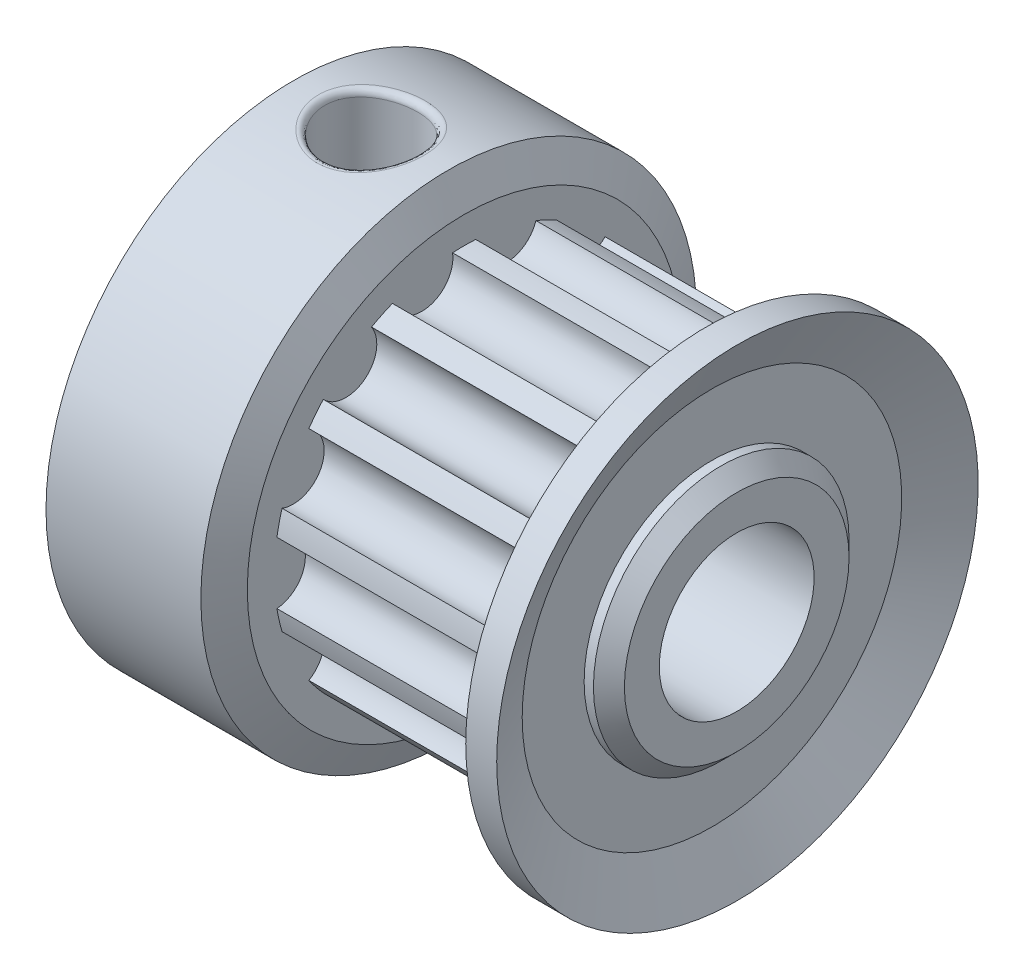
SolidWorks part; units mm, degrees
ref_plane "Ön Düzlem" through (0, 0, 0) normal (0, 0, 1) x (1, 0, 0)
ref_plane "Üst Düzlem" through (0, 0, 0) normal (0, 1, 0) x (1, 0, 0)
ref_plane "Sağ Düzlem" through (0, 0, 0) normal (1, 0, 0) x (0, 0, -1)
sketch "Çizim1" plane through (0, 0, 0) normal (0, 0, 1) x (1, 0, 0)
  line L0 (0, 9.9827) -> (0, -9.9827) construction
  line L1 (0, 0) -> (29.9605, 0) construction
  line L2 (0, 7) -> (0, 3.9)
  line L3 (0.1, 3.8) -> (0.3, 3.8)
  line L4 (0.3, 3.8) -> (0, 3.5)
  line L5 (0, 3.5) -> (0, 0)
  line L6 (0, 0) -> (14.8, 0)
  line L7 (14.8, 0) -> (14.8, 1.8873)
  line L10 (0, 7) -> (0.5, 8)
  line L11 (0.5, 8) -> (5.5, 8)
  line L12 (5.5, 8) -> (6, 7)
  line L13 (6, 7) -> (6, 6.1264)
  line L14 (6, 6.1264) -> (13, 6.1264)
  line L15 (13, 6.1264) -> (13.8229, 7.7721)
  line L18 (13.8229, 7.7721) -> (14.8229, 7.7721)
  line L19 (14.8229, 7.7721) -> (14, 6.1264)
  line L24 (14.8, 3.6264) -> (14.8, 1.8873)
  line L25 (14, 6.1264) -> (14, 4.1264)
  line L26 (14, 4.1264) -> (14.3, 4.1264)
  line L27 (14.3, 4.1264) -> (14.8, 3.6264)
  arc A0 (0, 3.9) -> (0.1, 3.8) centre (0.1, 3.9) ccw
  point P4 (0, 0)
  point P9 (14.8, 4.1264)
  point P33 (0, 3.8)
  dimension "D13" = 0.1
  dimension "D1" = 14.8
  dimension "D2" = 1
  dimension "D3" = 8
  dimension "D4" = 1.84
  dimension "D5" = 5
  dimension "D6" = 6
  dimension "D7" = 0.5
  dimension "D8" = 0.5
  dimension "D9" = 1
  dimension "D10" = 3.2
  dimension "D11" = 0.3
  dimension "D12" = 0.3
  dimension "D14" = 7
  dimension "D15" = 2
revolve "Döndür1" add sketch "Çizim1" angle 360 about L6
sketch "Çizim2" plane through (0, 0, 0) normal (-1, 0, 0) x (0, 0, 1)
  circle A0 centre (0, 0) radius 2.5
  dimension "D1" = 5
extrude "Kes-Ekstrüzyon1" cut sketch "Çizim2" against normal through all
sketch "Çizim3" plane through (6, 0, 0) normal (1, 0, 0) x (0, 0, -1)
  line L0 (0, 0) -> (6.1264, 0) construction
  circle A0 centre (0, 0) radius 6.1264 construction
  circle A1 centre (6.1264, 0) radius 1
  circle A2 centre (5.5197, -2.6581) radius 1
  circle A3 centre (3.8197, -4.7898) radius 1
  circle A4 centre (1.3632, -5.9728) radius 1
  circle A5 centre (-1.3632, -5.9728) radius 1
  circle A6 centre (-3.8197, -4.7898) radius 1
  circle A7 centre (-5.5197, -2.6581) radius 1
  circle A8 centre (-6.1264, 0) radius 1
  circle A9 centre (-5.5197, 2.6581) radius 1
  circle A10 centre (-3.8197, 4.7898) radius 1
  circle A11 centre (-1.3632, 5.9728) radius 1
  circle A12 centre (1.3632, 5.9728) radius 1
  circle A13 centre (3.8197, 4.7898) radius 1
  circle A14 centre (5.5197, 2.6581) radius 1
  point P35 (0, 0)
  dimension "D1" = 2
  dimension "D2" = 14
extrude "Kes-Ekstrüzyon3" cut sketch "Çizim3" along normal blind 7
sketch "Çizim4" plane through (0, 0, 0) normal (0, 1, 0) x (1, 0, 0)
  line L0 (0, 0) -> (5.5, 0) construction
  line L1 (0, 7) -> (0, -7) construction
  line L2 (5.5, -8) -> (5.5, 8) construction
  circle A0 centre (3, 0) radius 1.5
  dimension "D1" = 3
  dimension "D2" = 3
extrude "Kes-Ekstrüzyon4" cut sketch "Çizim4" along normal blind 27
fillet "Radyus1" radius 0.2 2 edges at (3.3158, 7.8645, 1.4664) (3.0032, 2, 1.5)
